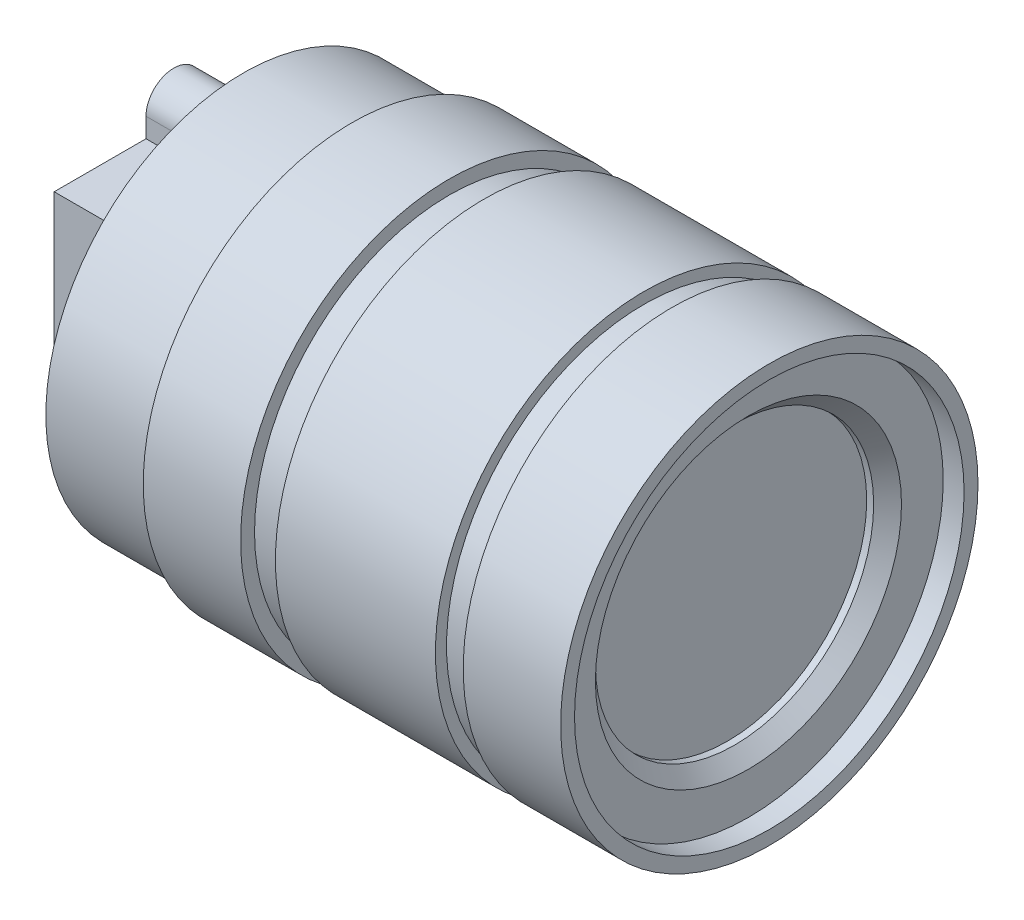
SolidWorks part; units mm, degrees
ref_plane "Plan XY" through (0, 0, 0) normal (0, 0, 1) x (1, 0, 0)
ref_plane "Plan ZX" through (0, 0, 0) normal (0, 1, 0) x (1, 0, 0)
ref_plane "Plan YZ" through (0, 0, 0) normal (1, 0, 0) x (0, 0, -1)
sketch "Esquisse1" plane through (0, 0, 0) normal (1, 0, 0) x (0, 0, -1)
  line L1 (8.6, -8.6) -> (-8.6, -8.6)
  line L2 (8.6, -8.6) -> (8.6, 8.6)
  line L3 (8.6, 8.6) -> (-8.6, 8.6)
  line L4 (-8.6, -8.6) -> (-8.6, 8.6)
  line L5 (8.6, -8.6) -> (-8.6, 8.6) construction
  line L6 (8.6, 8.6) -> (-8.6, -8.6) construction
  point P0 (0, 0)
  dimension "D1" = 17.2
extrude "Boss.-Extru.1" add sketch "Esquisse1" along normal blind 5
sketch "Esquisse2" plane through (0, 0, 0) normal (1, 0, 0) x (0, 0, -1)
  line L0 (-2, 8.6) -> (-2, 10)
  line L1 (8.6, 8.6) -> (-8.6, 8.6) construction
  line L2 (-2, 8.6) -> (2, 8.6)
  line L3 (2, 8.6) -> (2, 10)
  line L4 (0, 0) -> (0, 10) construction
  arc A0 (-2, 10) -> (2, 10) centre (0, 10) cw
  circle A1 centre (0, 10) radius 1
  point P8 (2, 9.3)
  dimension "D1" = 10
  dimension "D3" = 2
  dimension "D2" = 4
extrude "Boss.-Extru.2" add sketch "Esquisse2" along normal up to surface (5 mm away) up to face at (5, 0, 0)
mirror "Symétrie1" about plane through (0, 0, 0) normal (0, 1, 0) of "Boss.-Extru.2"
sketch "Esquisse3" plane through (5, 0, 0) normal (1, 0, 0) x (0, 0, -1)
  circle A0 centre (0, 0) radius 14.2
  dimension "D1" = 28.4
extrude "Boss.-Extru.3" add sketch "Esquisse3" along normal blind 7.8
sketch "Esquisse4" plane through (12.8, 0, 0) normal (1, 0, 0) x (0, 0, -1)
  circle A0 centre (0, 0) radius 15
  dimension "D1" = 30
extrude "Boss.-Extru.4" add sketch "Esquisse4" along normal blind 7
sketch "Esquisse5" plane through (19.8, 0, 0) normal (1, 0, 0) x (0, 0, -1)
  circle A0 centre (0, 0) radius 14
  dimension "D1" = 28
extrude "Boss.-Extru.5" add sketch "Esquisse5" along normal blind 2.5
sketch "Esquisse6" plane through (22.3, 0, 0) normal (1, 0, 0) x (0, 0, -1)
  circle A0 centre (0, 0) radius 15
  circle A1 centre (0, 0) radius 15 construction
extrude "Boss.-Extru.6" add sketch "Esquisse6" along normal blind 11.5
sketch "Esquisse7" plane through (33.8, 0, 0) normal (1, 0, 0) x (0, 0, -1)
  circle A0 centre (0, 0) radius 14.2
  circle A1 centre (0, 0) radius 14.2 construction
extrude "Boss.-Extru.7" add sketch "Esquisse7" along normal blind 2
sketch "Esquisse8" plane through (35.8, 0, 0) normal (1, 0, 0) x (0, 0, -1)
  circle A0 centre (0, 0) radius 15
  circle A1 centre (0, 0) radius 15 construction
extrude "Boss.-Extru.8" add sketch "Esquisse8" along normal blind 7
sketch "Esquisse9" plane through (42.8, 0, 0) normal (1, 0, 0) x (0, 0, -1)
  circle A0 centre (0, 0) radius 14
  dimension "D1" = 28
extrude "Enlèv. mat.-Extru.1" cut sketch "Esquisse9" against normal blind 1.5
sketch "Esquisse10" plane through (41.3, 0, 0) normal (1, 0, 0) x (0, 0, -1)
  circle A0 centre (0, 0) radius 10
  dimension "D1" = 20
extrude "Enlèv. mat.-Extru.2" cut sketch "Esquisse10" against normal blind 1.5
chamfer "Chanfrein1" distance 1 angle 45 1 edges at (41.3, 0, -10)
